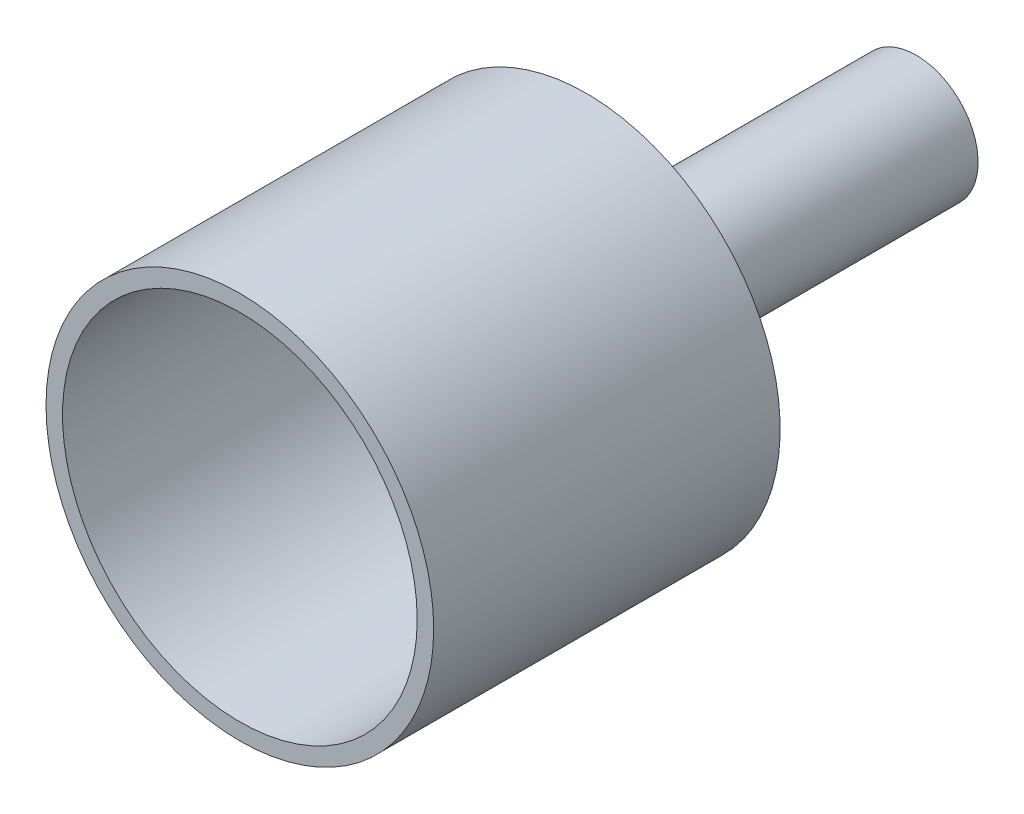
SolidWorks part; units mm, degrees
ref_plane "Front Plane" through (0, 0, 0) normal (0, 0, 1) x (1, 0, 0)
ref_plane "Top Plane" through (0, 0, 0) normal (0, 1, 0) x (1, 0, 0)
ref_plane "Right Plane" through (0, 0, 0) normal (1, 0, 0) x (0, 0, -1)
sketch "Sketch1" plane through (0, 0, 0) normal (0, 0, 1) x (1, 0, 0)
  circle A0 centre (0, 0) radius 23.5
  circle A1 centre (0, 0) radius 21.5
  dimension "D1" = 47
  dimension "D2" = 43
extrude "Boss-Extrude1" add sketch "Sketch1" along normal blind 40
ref_plane "Plane1" through (0, 23.5, 0) normal (0, 1, 0) x (1, 0, 0)
sketch "Sketch3" plane through (0, 0, 0) normal (0, 0, -1) x (-1, 0, 0)
  circle A0 centre (0, 0) radius 23.5
extrude "Boss-Extrude4" add sketch "Sketch3" along normal blind 2
sketch "Sketch4" plane through (0, 0, -2) normal (0, 0, -1) x (-1, 0, 0)
  circle A0 centre (0, 0) radius 7.5
  circle A1 centre (0, 0) radius 5.5
  dimension "D1" = 11
  dimension "D2" = 15
extrude "Boss-Extrude5" add sketch "Sketch4" along normal blind 40
sketch "Sketch5" plane through (0, 0, -2) normal (0, 0, -1) x (-1, 0, 0)
  circle A0 centre (0, 0) radius 5.5
  dimension "D1" = 11
extrude "Cut-Extrude1" cut sketch "Sketch5" against normal through all both and the other way through all
